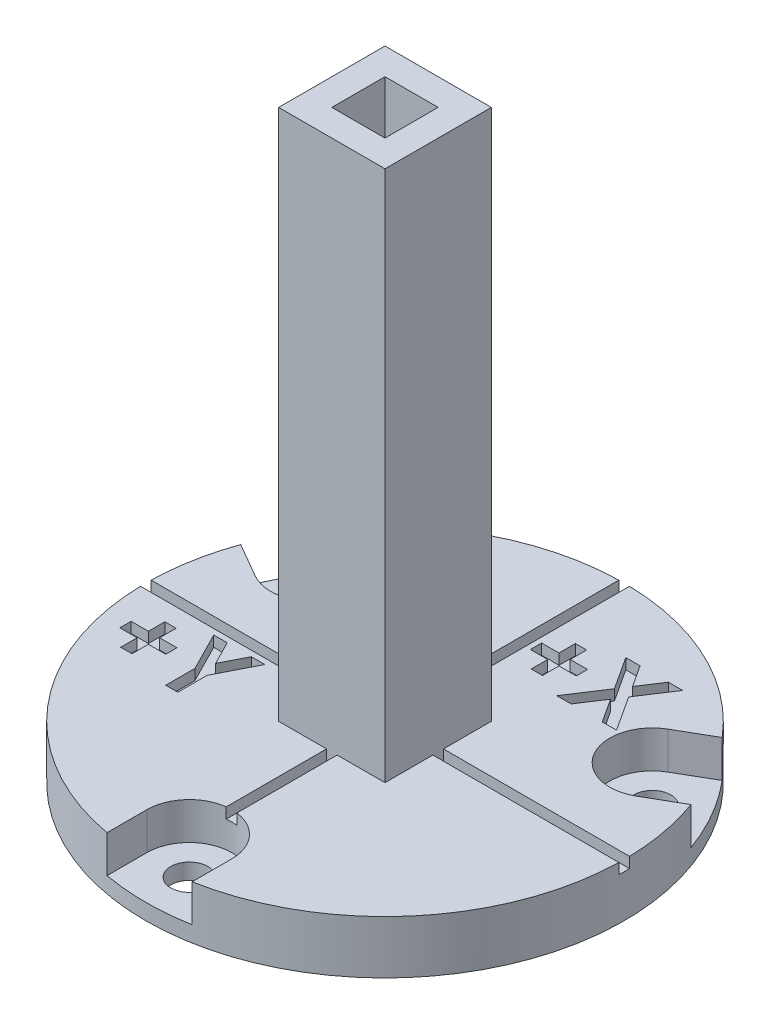
SolidWorks part; units mm, degrees
ref_plane "Front" through (0, 0, 0) normal (0, 0, 1) x (1, 0, 0)
ref_plane "Top" through (0, 0, 0) normal (0, 1, 0) x (1, 0, 0)
ref_plane "Right" through (0, 0, 0) normal (1, 0, 0) x (0, 0, -1)
sketch "Sketch1" plane through (0, 0, 0) normal (0, 1, 0) x (1, 0, 0)
  line L0 (0, 22.5) -> (0, -22.5) construction
  line L1 (22.5, 0) -> (-22.5, 0) construction
  circle A0 centre (0, 0) radius 22.5
  circle A1 centre (0, 0) radius 18.4 construction
  arc A2 (-10.9795, -19.6393) -> (-7.9114, -21.0632) centre (-9.4455, -20.3512) cw construction
  point P19 (0, 0)
  dimension "D1" = 45
  dimension "D2" = 36.8
extrude "plate" add sketch "Sketch1" along normal blind 5
sketch "Sketch6" plane through (0, 5, 0) normal (0, 1, 0) x (1, 0, 0)
  line L0 (0, 22.5) -> (0, -22.5) construction
  line L1 (0, -22.5) -> (0, -18.4) construction
  line L2 (-4, -22.5) -> (-4, -18.4)
  line L3 (4, -22.5) -> (4, -18.4)
  circle A1 centre (0, 0) radius 18.4 construction
  circle A2 centre (0, 0) radius 22.5 construction
  arc A3 (-4, -22.5) -> (4, -22.5) centre (0, -22.5) ccw
  arc A4 (4, -18.4) -> (-4, -18.4) centre (0, -18.4) ccw
  point P7 (0, -20.45)
  dimension "D1" = 4
extrude "opening for screw" cut sketch "Sketch6" against normal blind 5 from offset 1.5 contours L3 A4 L2 A3
sketch "Sketch7" plane through (0, 1.5, 0) normal (0, 1, 0) x (1, 0, 0)
  line L0 (0, 22.5) -> (0, -22.5) construction
  circle A0 centre (0, -18.4) radius 1.75
  circle A1 centre (0, 0) radius 18.4 construction
  dimension "D1" = 3.5
extrude "screw hole" cut sketch "Sketch7" against normal blind 5
pattern_circular "CirPattern20" count 3 over 360 about axis through (0, 0, 0) along (0, 1, 0) of "opening for screw", "screw hole"
sketch "Sketch10" plane through (0, 5, 0) normal (0, 1, 0) x (1, 0, 0)
  line L1 (-22.5, 0.5) -> (22.5, 0.5)
  line L2 (-22.5, 0.5) -> (-22.5, -0.5)
  line L3 (-22.5, -0.5) -> (22.5, -0.5)
  line L4 (22.5, 0.5) -> (22.5, -0.5)
  line L5 (-0.5, 22.5) -> (0.5, 22.5)
  line L6 (-0.5, 22.5) -> (-0.5, -22.5)
  line L7 (-0.5, -22.5) -> (0.5, -22.5)
  line L8 (0.5, 22.5) -> (0.5, -22.5)
  line L9 (0, 22.5) -> (0, -22.5) construction
  point P4 (22.5, 0)
  point P9 (-22.5, 0)
  point P14 (0, -22.5)
  point P15 (0, 22.5)
  dimension "D1" = 1
  dimension "D2" = 1
extrude "Cut-Extrude5" cut sketch "Sketch10" against normal blind 1 contours L6 L7 L8 L5 | L1 L4 L3 L2
sketch "Sketch11" plane through (0, 5, 0) normal (0, 1, 0) x (1, 0, 0)
  line L0 (0.5, 22.4944) -> (0.5, 0.5) construction
  text T0 "<b>+X</b>"
  text T1 "<b>+Y</b>"
extrude "Cut-Extrude6" cut sketch "Sketch11" against normal blind 1
sketch "Sketch12" plane through (0, 5, 0) normal (0, 1, 0) x (1, 0, 0)
  line L0 (0, 5) -> (0, -5) construction
  line L1 (-5, 5) -> (5, 5)
  line L2 (-5, 5) -> (-5, -5)
  line L3 (-5, -5) -> (5, -5)
  line L4 (5, 5) -> (5, -5)
  line L5 (-5, 0) -> (5, 0) construction
  line L9 (-2.5, 2.5) -> (2.5, 2.5)
  line L10 (-2.5, 2.5) -> (-2.5, -2.5)
  line L11 (-2.5, -2.5) -> (2.5, -2.5)
  line L12 (2.5, 2.5) -> (2.5, -2.5)
  point P8 (0, 0)
  point P9 (0, 0)
  point P15 (2.9741, 2.629)
  point P16 (2.6408, 2.6408)
  dimension "D1" = 10
  dimension "D2" = 5
extrude "tool connect piece" add sketch "Sketch12" along normal blind 50 and the other way up to surface (1 mm away) contours L9 L12 L11 L10 | L4 L3 L2 L1
